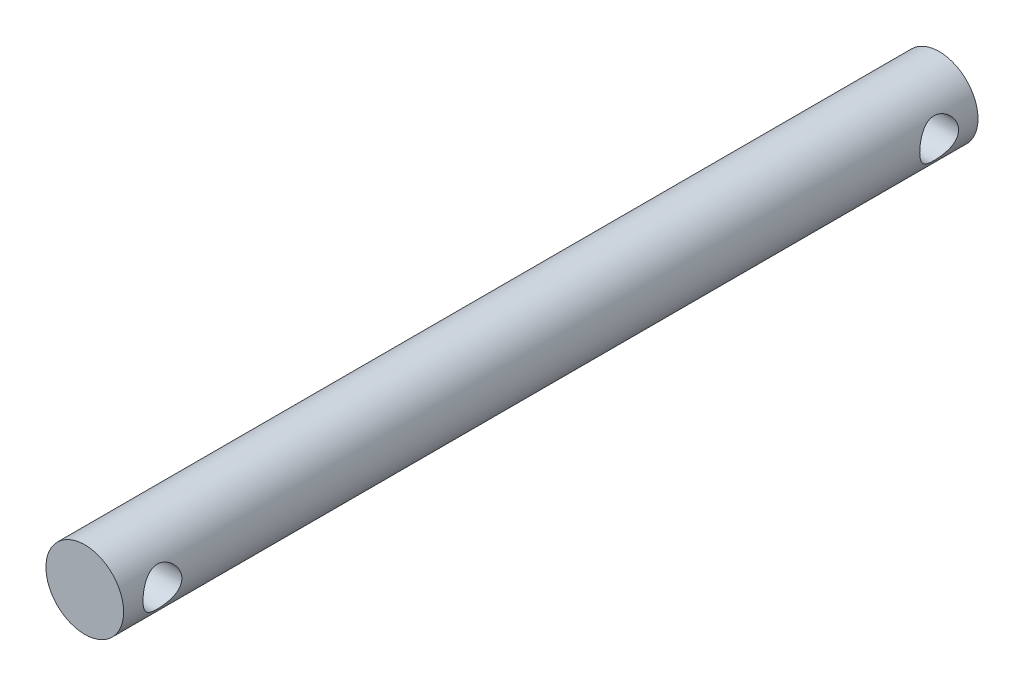
SolidWorks part; units mm, degrees
ref_plane "前基準面" through (0, 0, 0) normal (0, 0, 1) x (1, 0, 0)
ref_plane "上基準面" through (0, 0, 0) normal (0, 1, 0) x (1, 0, 0)
ref_plane "右基準面" through (0, 0, 0) normal (1, 0, 0) x (0, 0, -1)
sketch "草圖1" plane through (0, 0, 0) normal (0, 0, 1) x (1, 0, 0)
  circle A0 centre (0, 0) radius 3
  dimension "D1" = 6
extrude "填料-伸長1" add sketch "草圖1" along normal mid plane 66
sketch "草圖2" plane through (0, 0, 0) normal (1, 0, 0) x (0, 0, -1)
  line L0 (33, -3) -> (33, 3) construction
  line L1 (0, 8.7271) -> (0, -9.5389) construction
  circle A0 centre (30, 0) radius 1.5
  circle A1 centre (-30, 0) radius 1.5
  dimension "D1" = 3
  dimension "D2" = 3
extrude "除料-伸長1" cut sketch "草圖2" against normal mid plane 66
